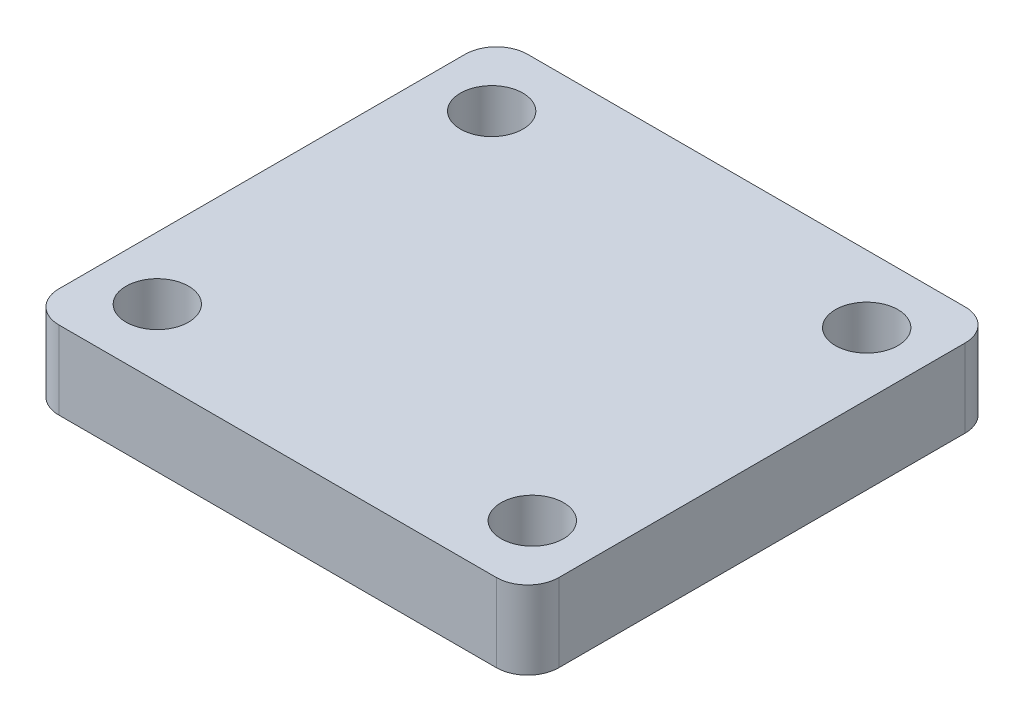
SolidWorks part; units mm, degrees
ref_plane "Front Plane" through (0, 0, 0) normal (0, 0, 1) x (1, 0, 0)
ref_plane "Top Plane" through (0, 0, 0) normal (0, 1, 0) x (1, 0, 0)
ref_plane "Right Plane" through (0, 0, 0) normal (1, 0, 0) x (0, 0, -1)
sketch "Sketch1" plane through (0, 0, 0) normal (0, 1, 0) x (1, 0, 0)
  line L1 (14, -15) -> (-14, -15)
  line L2 (16, -13) -> (16, 13)
  line L3 (14, 15) -> (-14, 15)
  line L4 (-16, -13) -> (-16, 13)
  line L5 (16, -15) -> (-16, 15) construction
  line L6 (16, 15) -> (-16, -15) construction
  arc A0 (-16, -13) -> (-14, -15) centre (-14, -13) ccw
  arc A1 (16, -13) -> (14, -15) centre (14, -13) cw
  arc A2 (16, 13) -> (14, 15) centre (14, 13) ccw
  arc A3 (-14, 15) -> (-16, 13) centre (-14, 13) ccw
  point P0 (0, 0)
  dimension "D3" = 2
  dimension "D1" = 32
  dimension "D2" = 30
extrude "5" add sketch "Sketch1" along normal blind 5
sketch "Sketch2" plane through (0, 5, 0) normal (0, 1, 0) x (1, 0, 0)
  line L0 (0, -55) -> (0, 55) construction
  line L1 (-55, 0) -> (55, 0) construction
  circle A0 centre (-12, 10.7) radius 2
  circle A1 centre (12, 10.7) radius 2
  circle A2 centre (12, -10.7) radius 2
  circle A3 centre (-12, -10.7) radius 2
  dimension "D1" = 12
  dimension "D2" = 10.7
extrude "Cut-Extrude1" cut sketch "Sketch2" against normal blind 5
